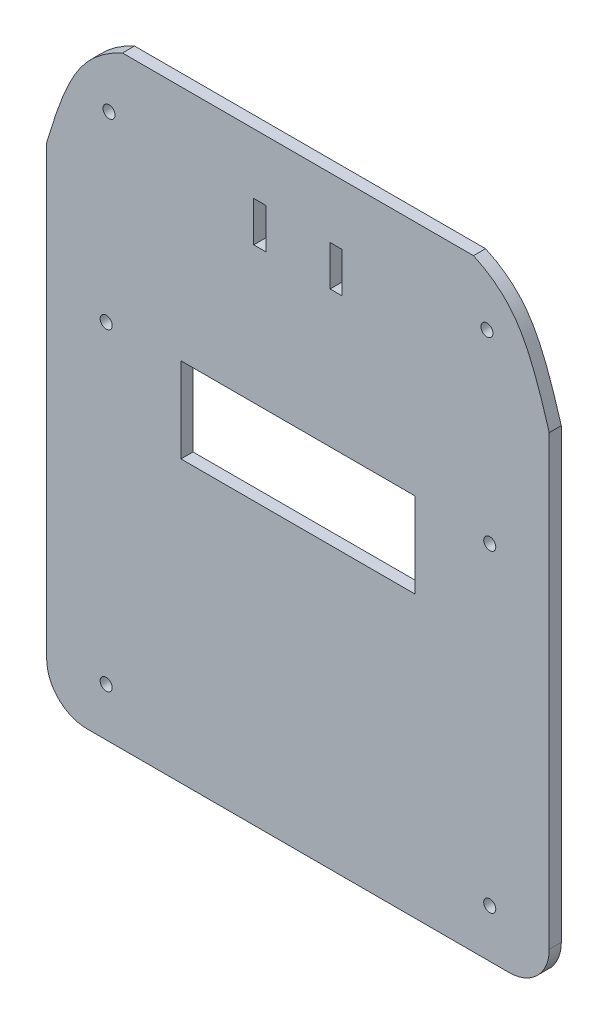
SolidWorks part; units mm, degrees
ref_plane "Front Plane" through (0, 0, 0) normal (0, 0, 1) x (1, 0, 0)
ref_plane "Top Plane" through (0, 0, 0) normal (0, 1, 0) x (1, 0, 0)
ref_plane "Right Plane" through (0, 0, 0) normal (1, 0, 0) x (0, 0, -1)
sketch "Sketch1" plane through (0, 0, 0) normal (0, 0, 1) x (1, 0, 0)
  line L1 (0, 0) -> (125, 0)
  line L2 (0, 0) -> (0, 150)
  line L3 (0, 150) -> (125, 150)
  line L4 (125, 0) -> (125, 150)
  dimension "D1" = 125
  dimension "D2" = 150
extrude "Boss-Extrude1" add sketch "Sketch1" along normal blind 3
sketch "Sketch6" plane through (0, 0, 0) normal (0, 0, -1) x (-1, 0, 0)
  line L0 (-62.5, 150) -> (-62.5, 0) construction
  line L1 (-125, 150) -> (0, 150) construction
  line L2 (0, 0) -> (-125, 0) construction
  circle A0 centre (-15.5, 135.6782) radius 1.5
  circle A1 centre (-109.5, 135.6782) radius 1.5
  dimension "D1" = 3
  dimension "D2" = 47
extrude "Cut-Extrude5" cut sketch "Sketch6" against normal through all
sketch "Sketch7" plane through (0, 0, 3) normal (0, 0, 1) x (1, 0, 0)
  line L0 (0, 150) -> (0, 0) construction
  line L1 (0, 121.3038) -> (5.1307, 138.5541) construction
  line L2 (5.1307, 138.5541) -> (8.0571, 143.1747) construction
  line L3 (8.0571, 143.1747) -> (13.2938, 147.4873) construction
  line L4 (13.2938, 147.4873) -> (18.8386, 150) construction
  line L5 (125, 150) -> (0, 150) construction
  line L6 (18.8386, 150) -> (0, 150)
  line L7 (0, 150) -> (0, 121.3038)
  line L8 (62.5, 150) -> (62.5, 0) construction
  line L9 (0, 0) -> (125, 0) construction
  line L10 (125, 121.3038) -> (119.8693, 138.5541) construction
  line L11 (119.8693, 138.5541) -> (116.9429, 143.1747) construction
  line L12 (116.9429, 143.1747) -> (111.7062, 147.4873) construction
  line L13 (111.7062, 147.4873) -> (106.1614, 150) construction
  line L14 (125, 150) -> (125, 121.3038)
  line L15 (106.1614, 150) -> (125, 150)
  spline S0 degree 4 poles (0, 121.3038) (5.1307, 138.5541) (8.0571, 143.1747) (13.2938, 147.4873) (18.8386, 150) knots 0 0 0 0 0 1 1 1 1 1
  spline S1 degree 4 poles (125, 121.3038) (119.8693, 138.5541) (116.9429, 143.1747) (111.7062, 147.4873) (106.1614, 150) knots 0 0 0 0 0 1 1 1 1 1
extrude "Cut-Extrude6" cut sketch "Sketch7" against normal through all
sketch "Sketch8" plane through (0, 0, 3) normal (0, 0, 1) x (1, 0, 0)
  line L0 (0, 0) -> (125, 0) construction
  line L2 (62.5, 150) -> (62.5, 0) construction
  line L3 (106.1614, 150) -> (18.8386, 150) construction
  circle A0 centre (14.8, 12) radius 1.5
  circle A1 centre (110.2, 12) radius 1.5
  circle A2 centre (14.8, 90) radius 1.5
  circle A3 centre (110.2, 90) radius 1.5
  dimension "D1" = 3
  dimension "D2" = 12
  dimension "D3" = 47.7
  dimension "D4" = 3
  dimension "D5" = 78
extrude "Cut-Extrude7" cut sketch "Sketch8" against normal through all
fillet "Fillet1" radius 10 2 edges at (125, 0, 1.5) (0, 0, 1.5)
sketch "Sketch10" plane through (0, 0, 3) normal (0, 0, 1) x (1, 0, 0)
  line L0 (106.1614, 150) -> (18.8386, 150) construction
  line L1 (33.4014, 90.9737) -> (91.5986, 90.9737)
  line L2 (33.4014, 90.9737) -> (33.4014, 69.8344)
  line L3 (33.4014, 69.8344) -> (91.5986, 69.8344)
  line L4 (91.5986, 90.9737) -> (91.5986, 69.8344)
  point P4 (62.5, 90.9737)
  point P7 (62.5, 150)
extrude "Cut-Extrude8" cut sketch "Sketch10" against normal through all
sketch "Sketch11" plane through (0, 0, 3) normal (0, 0, 1) x (1, 0, 0)
  line L0 (62.5, 150) -> (62.5, 0) construction
  line L1 (106.1614, 150) -> (18.8386, 150) construction
  line L2 (10, 0) -> (115, 0) construction
  line L3 (70.5, 125) -> (70.5, 135)
  line L4 (51.5, 125) -> (54.5, 125)
  line L5 (51.5, 125) -> (51.5, 135)
  line L6 (51.5, 135) -> (54.5, 135)
  line L7 (54.5, 125) -> (54.5, 135)
  line L8 (73.5, 135) -> (70.5, 135)
  line L9 (73.5, 125) -> (73.5, 135)
  line L10 (73.5, 125) -> (70.5, 125)
  dimension "D1" = 10
  dimension "D2" = 3
  dimension "D3" = 8
  dimension "D4" = 15
extrude "Cut-Extrude9" cut sketch "Sketch11" against normal through all
